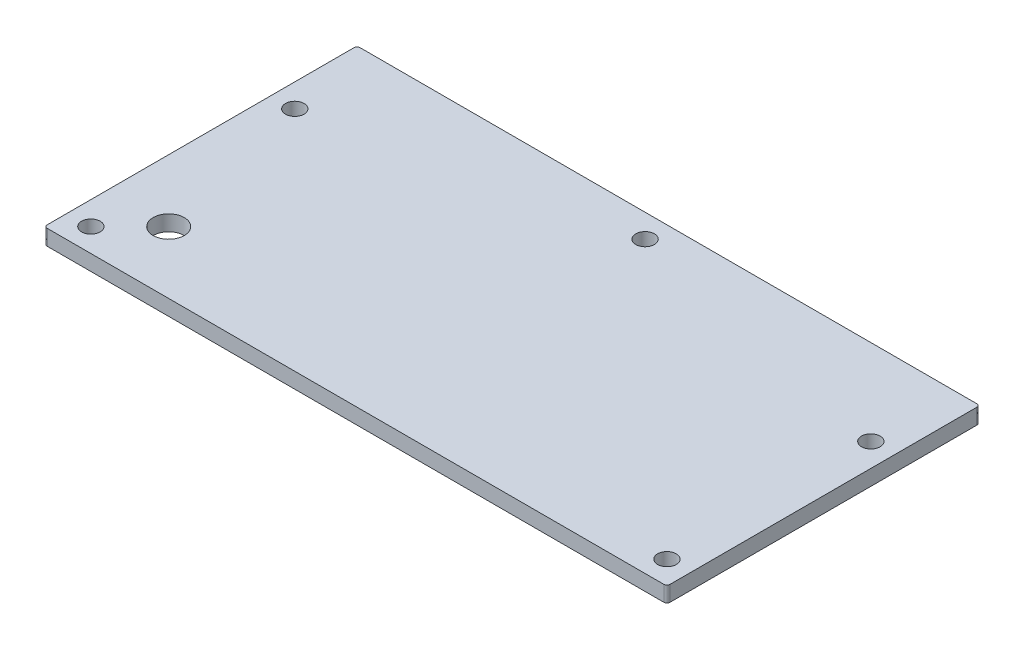
SolidWorks part; units mm, degrees
material "Alum Plate"
ref_plane "Front Plane" through (0, 0, 0) normal (0, 0, 1) x (1, 0, 0)
ref_plane "Top Plane" through (0, 0, 0) normal (0, 1, 0) x (1, 0, 0)
ref_plane "Right Plane" through (0, 0, 0) normal (1, 0, 0) x (0, 0, -1)
other "Bounding Box"
ref_plane "Default Plane" through (13.8565, 3.175, 6.7999) normal (0, -1, 0) x (-1, 0, 0)
sketch "Sketch1" plane through (0, 0, 0) normal (0, 1, 0) x (1, 0, 0)
  line L1 (-63.5, -31.9024) -> (63.5, -31.9024)
  line L2 (-63.5, -31.9024) -> (-63.5, 31.9024)
  line L3 (-63.5, 31.9024) -> (63.5, 31.9024)
  line L4 (63.5, -31.9024) -> (63.5, 31.9024)
  line L5 (-63.5, -31.9024) -> (63.5, 31.9024) construction
  line L6 (-63.5, 31.9024) -> (63.5, -31.9024) construction
  point P0 (0, 0)
  dimension "D1" = 127
  dimension "D2" = 63.8048
extrude "Boss-Extrude1" add sketch "Sketch1" along normal blind 3.175
sketch "Sketch2" plane through (0, 3.175, 0) normal (0, 1, 0) x (1, 0, 0)
  line L0 (63.5, -31.9024) -> (63.5, 31.9024) construction
  line L1 (-63.5, 31.9024) -> (63.5, 31.9024)
  line L2 (-63.5, 31.9024) -> (-63.5, 31.5976)
  line L3 (-63.5, 31.5976) -> (63.5, 31.5976)
  line L4 (63.5, 31.9024) -> (63.5, 31.5976)
  line L5 (-63.5, 31.9024) -> (63.5, 31.5976) construction
  line L6 (-63.5, 31.5976) -> (63.5, 31.9024) construction
  line L7 (-63.5, -31.9024) -> (63.5, -31.9024) construction
  point P4 (0, 31.75)
  dimension "D1" = 63.5
extrude "Cut-Extrude1" [suppressed] cut sketch "Sketch2" against normal through all
sketch "Sketch3" [suppressed] plane through (0, 3.175, 0) normal (0, 1, 0) x (1, 0, 0)
  line L0 (58.7375, -31.9024) -> (58.7375, -27.1399) construction
  line L1 (-63.5, -31.9024) -> (63.5, -31.9024) construction
  line L2 (58.7375, -27.1399) -> (-58.7375, -27.1399) construction
  line L3 (-58.7375, -27.1399) -> (-58.7375, 26.8351) construction
  line L4 (-58.7375, 26.8351) -> (58.7375, 26.8351) construction
  line L5 (58.7375, 26.8351) -> (58.7375, -27.1399) construction
  line L6 (58.7375, -27.1399) -> (63.5, -27.1399) construction
  line L7 (63.5, -31.9024) -> (63.5, 31.5976) construction
  line L8 (-58.7375, 26.8351) -> (-63.5, 26.8351) construction
  line L9 (-63.5, 31.5976) -> (-63.5, -31.9024) construction
  line L10 (-58.7375, 26.8351) -> (-58.7375, 31.5976) construction
  line L11 (-63.5, 31.5976) -> (63.5, 31.5976) construction
  line L12 (-36.5125, -27.1399) -> (-36.5125, -29.0449) construction
  line L13 (-36.5125, -29.0449) -> (-14.2875, -29.0449) construction
  line L14 (-14.2875, -29.0449) -> (14.2875, -29.0449) construction
  line L15 (14.2875, -29.0449) -> (36.5125, -29.0449) construction
  line L16 (36.5125, -29.0449) -> (36.5125, -27.1399) construction
  line L17 (0, -29.0449) -> (0, 0) construction
  circle A0 centre (-58.7375, -27.1399) radius 1.8986
  circle A1 centre (-58.7375, 26.8351) radius 1.8986
  circle A2 centre (58.7375, 26.8351) radius 1.8986
  circle A3 centre (58.7375, -27.1399) radius 1.8986
  circle A5 centre (-36.5125, -29.0449) radius 1.8986
  circle A6 centre (-14.2875, -29.0449) radius 1.8986
  circle A7 centre (14.2875, -29.0449) radius 1.8987
  circle A8 centre (36.5125, -29.0449) radius 1.8986
  dimension "D2" = 3.7973
  dimension "D1" = 4.7625
  dimension "D3" = 22.225
  dimension "D4" = 28.575
  dimension "D5" = 1.905
extrude "Cut-Extrude2" [suppressed] cut sketch "Sketch3" against normal through all
sketch "Sketch4" plane through (0, 3.175, 0) normal (0, 1, 0) x (1, 0, 0)
  line L0 (58.7375, -27.1399) -> (58.7375, 14.4399) construction
  line L1 (58.7375, 14.4399) -> (-58.7375, 14.4399) construction
  line L2 (-58.7375, 14.4399) -> (-58.7375, -27.1399) construction
  line L3 (-58.7375, -27.1399) -> (58.7375, -27.1399) construction
  line L4 (58.7375, -27.1399) -> (58.7375, -31.9024) construction
  line L5 (-63.5, -31.9024) -> (63.5, -31.9024) construction
  line L6 (58.7375, -27.1399) -> (63.5, -27.1399) construction
  line L7 (63.5, -31.9024) -> (63.5, 31.9024) construction
  line L8 (-63.5, 14.4399) -> (-58.7375, 14.4399) construction
  line L9 (-63.5, 31.9024) -> (-63.5, -31.9024) construction
  line L10 (-58.7375, 14.4399) -> (-58.7375, 31.9024) construction
  line L11 (63.5, 31.9024) -> (-63.5, 31.9024) construction
  line L12 (0, 14.4399) -> (0, 27.1399) construction
  line L13 (0, 27.1399) -> (0, 31.9024) construction
  circle A0 centre (-58.7375, -27.1399) radius 1.8986
  circle A1 centre (-58.7375, 14.4399) radius 1.8986
  circle A2 centre (58.7375, 14.4399) radius 1.8986
  circle A3 centre (58.7375, -27.1399) radius 1.8986
  circle A4 centre (0, 27.1399) radius 1.8986
  dimension "D2" = 3.7973
  dimension "D1" = 4.7625
  dimension "D3" = 17.4625
  dimension "D4" = 4.7625
extrude "Cut-Extrude3" cut sketch "Sketch4" against normal through all
sketch "Sketch5" plane through (0, 3.175, 0) normal (0, 1, 0) x (1, 0, 0)
  line L0 (-53.975, -31.9024) -> (-53.975, 31.9024) construction
  line L5 (-63.5, -31.9024) -> (63.5, -31.9024) construction
  line L7 (63.5, 31.9024) -> (-63.5, 31.9024) construction
  line L11 (-63.5, 31.9024) -> (-63.5, -31.9024) construction
  line L17 (-53.975, -19.2024) -> (-50.8, -19.2024) construction
  circle A9 centre (-50.8, -19.2024) radius 3.175
  dimension "D1" = 9.525
  dimension "D2" = 3.175
  dimension "D3" = 6.35
  dimension "D4" = 12.7
extrude "Cut-Extrude4" cut sketch "Sketch5" against normal through all
fillet "Fillet2" radius 0.635 4 edges at (-63.5, 1.5875, 31.9024) (63.5, 1.5875, 31.9024) (63.5, 1.5875, -31.9024) (-63.5, 1.5875, -31.9024)
fillet "Fillet3" [suppressed] radius 0.635
